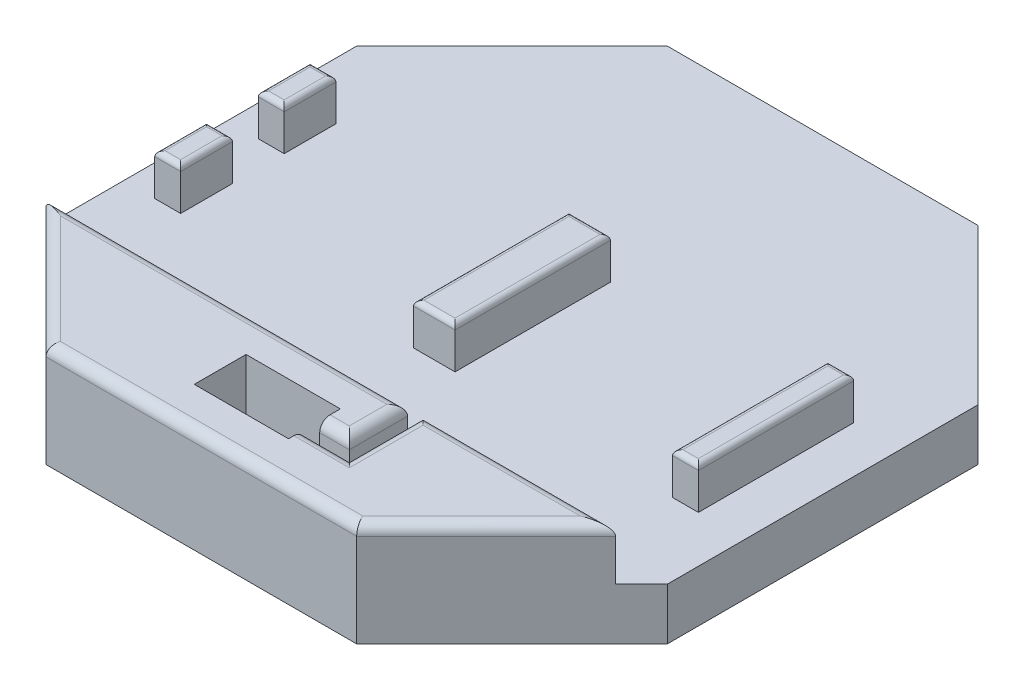
SolidWorks part; units mm, degrees
ref_plane "Front Plane" through (0, 0, 0) normal (0, 0, 1) x (1, 0, 0)
ref_plane "Top Plane" through (0, 0, 0) normal (0, 1, 0) x (1, 0, 0)
ref_plane "Right Plane" through (0, 0, 0) normal (1, 0, 0) x (0, 0, -1)
sketch "Sketch1" plane through (0, 0, 0) normal (0, 1, 0) x (1, 0, 0)
  line L0 (-38.1, 76.2) -> (38.1, 76.2)
  line L1 (38.1, 76.2) -> (76.2, 38.1)
  line L2 (76.2, 38.1) -> (76.2, -38.1)
  line L3 (76.2, -38.1) -> (38.1, -76.2)
  line L4 (38.1, -76.2) -> (-38.1, -76.2)
  line L5 (-38.1, -76.2) -> (-76.2, -38.1)
  line L6 (-76.2, -38.1) -> (-76.2, 38.1)
  line L7 (-76.2, 38.1) -> (-38.1, 76.2)
  line L8 (0, 76.2) -> (0, -76.2) construction
  point P10 (0, 0)
  point P11 (0, 0)
  dimension "D1" = 152.4
  dimension "D2" = 152.4
  dimension "D3" = 76.2
  dimension "D4" = 76.2
  dimension "D5" = 76.2
  dimension "D6" = 76.2
  dimension "D7" = 38.1
  dimension "D8" = 38.1
extrude "Boss-Extrude1" add sketch "Sketch1" along normal blind 12.7
sketch "Sketch2" plane through (0, 12.7, 0) normal (0, 1, 0) x (1, 0, 0)
  line L0 (0, 76.2) -> (0, -76.2) construction
  line L1 (38.1, 76.2) -> (-38.1, 76.2) construction
  line L2 (-38.1, -76.2) -> (38.1, -76.2) construction
  line L3 (-76.2, 19.05) -> (76.2, 19.05) construction
  line L4 (-5.08, -19.05) -> (5.08, -19.05)
  line L5 (-5.08, -19.05) -> (-5.08, 19.05)
  line L6 (-5.08, 19.05) -> (5.08, 19.05)
  line L7 (5.08, -19.05) -> (5.08, 19.05)
  line L8 (-5.08, -19.05) -> (5.08, 19.05) construction
  line L9 (-5.08, 19.05) -> (5.08, -19.05) construction
  line L10 (64.77, -19.05) -> (58.42, -19.05)
  line L11 (64.77, -19.05) -> (64.77, 19.05)
  line L12 (64.77, 19.05) -> (58.42, 19.05)
  line L13 (58.42, -19.05) -> (58.42, 19.05)
  line L14 (64.77, -19.05) -> (58.42, 19.05) construction
  line L15 (64.77, 19.05) -> (58.42, -19.05) construction
  line L16 (-76.2, 38.1) -> (-76.2, -38.1) construction
  line L17 (76.2, -38.1) -> (76.2, 38.1) construction
  line L19 (-68.58, 6.35) -> (-62.23, 6.35)
  line L20 (-68.58, 6.35) -> (-68.58, 19.05)
  line L21 (-68.58, 19.05) -> (-62.23, 19.05)
  line L22 (-62.23, 6.35) -> (-62.23, 19.05)
  line L23 (-68.58, 6.35) -> (-62.23, 19.05) construction
  line L24 (-68.58, 19.05) -> (-62.23, 6.35) construction
  line L25 (-68.58, -19.05) -> (-62.23, -19.05)
  line L26 (-68.58, -19.05) -> (-68.58, -6.35)
  line L27 (-68.58, -6.35) -> (-62.23, -6.35)
  line L28 (-62.23, -19.05) -> (-62.23, -6.35)
  line L29 (-68.58, -19.05) -> (-62.23, -6.35) construction
  line L30 (-68.58, -6.35) -> (-62.23, -19.05) construction
  point P6 (0, 0)
  point P12 (61.595, 0)
  point P23 (-65.405, 12.7)
  point P28 (-65.405, -12.7)
  point P33 (0, -19.05)
  dimension "D1" = 38.1
  dimension "D2" = 38.1
  dimension "D3" = 6.35
  dimension "D4" = 10.16
  dimension "D5" = 53.34
  dimension "D6" = 6.35
  dimension "D7" = 12.7
  dimension "D8" = 57.15
  dimension "D9" = 12.7
  dimension "D10" = 6.35
extrude "Boss-Extrude2" add sketch "Sketch2" along normal blind 10.16
sketch "Sketch4" plane through (0, 12.7, 0) normal (0, 1, 0) x (1, 0, 0)
  line L0 (0, 76.2) -> (0, -76.2) construction
  line L1 (38.1, 76.2) -> (-38.1, 76.2) construction
  line L2 (-38.1, -76.2) -> (38.1, -76.2) construction
  line L3 (-69.85, -44.45) -> (69.85, -44.45)
  line L4 (-76.2, -38.1) -> (-38.1, -76.2) construction
  line L5 (38.1, -76.2) -> (76.2, -38.1) construction
  line L6 (-69.85, -44.45) -> (-38.1, -76.2)
  line L7 (-38.1, -76.2) -> (38.1, -76.2)
  line L8 (38.1, -76.2) -> (69.85, -44.45)
  dimension "D1" = 31.75
extrude "Boss-Extrude3" add sketch "Sketch4" along normal blind 12.7
sketch "Sketch5" plane through (0, 25.4, 0) normal (0, 1, 0) x (1, 0, 0)
  line L0 (0, 0) -> (0, -76.2) construction
  line L1 (-38.1, -76.2) -> (38.1, -76.2) construction
  line L2 (11.557, -58.7213) -> (18.8293, -58.7213)
  line L3 (-11.557, -66.3738) -> (11.557, -66.3738)
  line L4 (-11.557, -66.3738) -> (-11.557, -53.6738)
  line L5 (-11.557, -53.6738) -> (11.557, -53.6738)
  line L6 (11.557, -58.7213) -> (11.557, -53.6738)
  line L7 (-11.557, -66.3738) -> (11.557, -53.6738) construction
  line L8 (-11.557, -53.6738) -> (11.557, -66.3738) construction
  line L9 (18.8293, -58.7213) -> (18.8293, -44.45)
  line L10 (69.85, -44.45) -> (-69.85, -44.45) construction
  line L11 (18.8293, -44.45) -> (22.6393, -44.45)
  line L12 (22.6393, -44.45) -> (22.6393, -62.5313)
  line L13 (22.6393, -62.5313) -> (11.557, -62.5313)
  line L14 (11.557, -62.5313) -> (11.557, -66.3738)
  point P5 (0, -60.0238)
  dimension "D1" = 12.7
  dimension "D2" = 23.114
  dimension "D3" = 3.81
  dimension "D4" = 3.81
extrude "Cut-Extrude1" cut sketch "Sketch5" against normal blind 15.24
fillet "Fillet2" radius 2.54 9 edges at (53.975, 25.4, 60.325) (46.2447, 25.4, 44.45) (0, 25.4, 76.2) (-53.975, 25.4, 60.325) (-25.5103, 25.4, 44.45) (15.1932, 25.4, 58.7213) (17.0982, 25.4, 62.5313) (22.6393, 25.4, 53.4907) (18.8293, 25.4, 51.5857)
fillet "Fillet4" radius 1.27 16 edges at (-65.405, 22.86, 19.05) (-68.58, 22.86, 12.7) (-65.405, 22.86, 6.35) (-62.23, 22.86, 12.7) (-65.405, 22.86, -6.35) (-68.58, 22.86, -12.7) (-65.405, 22.86, -19.05) (-62.23, 22.86, -12.7) (61.595, 22.86, -19.05) (64.77, 22.86, 0) (61.595, 22.86, 19.05) (58.42, 22.86, 0) (0, 22.86, 19.05) (-5.08, 22.86, 0) (0, 22.86, -19.05) (5.08, 22.86, 0)
sketch "Sketch8" plane through (18.8293, 0, 0) normal (1, 0, 0) x (0, 0, -1)
  line L0 (-58.7213, 10.16) -> (-44.45, 12.7)
  line L1 (-58.7213, 10.16) -> (-44.45, 10.16)
  line L2 (-44.45, 10.16) -> (-44.45, 12.7)
extrude "Boss-Extrude4" add sketch "Sketch8" along normal blind 3.81
